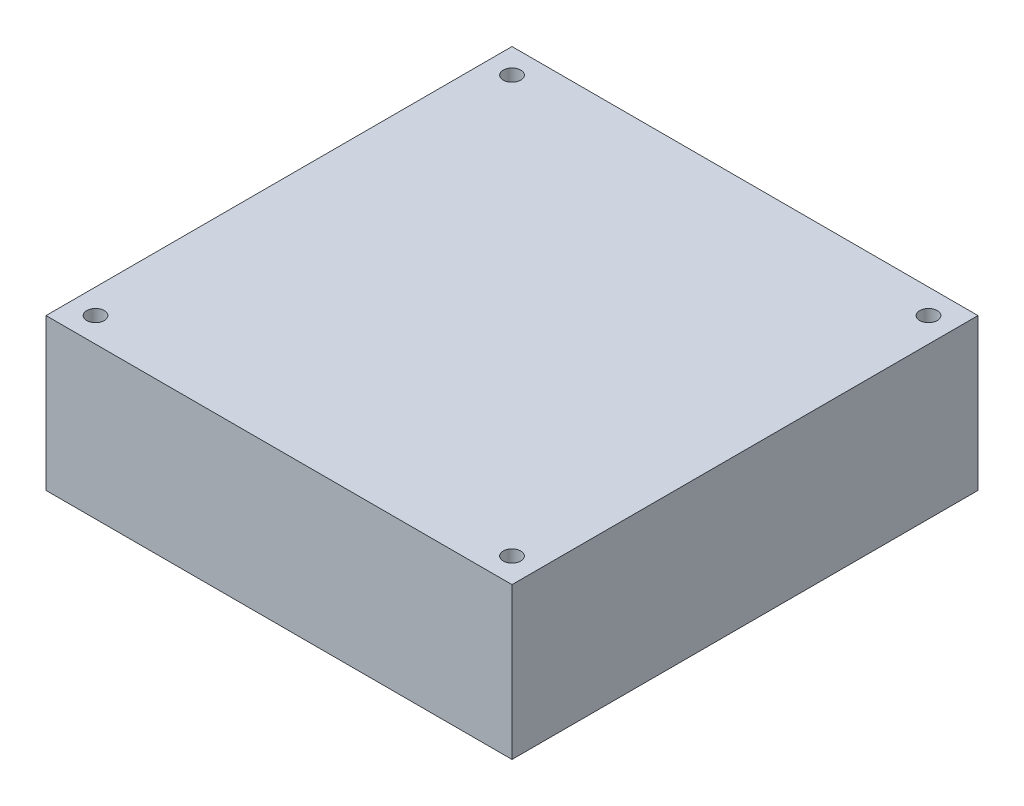
SolidWorks part; units mm, degrees
ref_plane "Front Plane" through (0, 0, 0) normal (0, 0, 1) x (1, 0, 0)
ref_plane "Top Plane" through (0, 0, 0) normal (0, 1, 0) x (1, 0, 0)
ref_plane "Right Plane" through (0, 0, 0) normal (1, 0, 0) x (0, 0, -1)
sketch "Sketch1" plane through (0, 0, 0) normal (0, 1, 0) x (1, 0, 0)
  line L1 (-40, -40) -> (40, -40)
  line L2 (-40, -40) -> (-40, 40)
  line L3 (-40, 40) -> (40, 40)
  line L4 (40, -40) -> (40, 40)
  line L5 (-40, -40) -> (40, 40) construction
  line L6 (-40, 40) -> (40, -40) construction
  line L7 (-35.75, -35.75) -> (35.75, -35.75) construction
  line L8 (-35.75, -35.75) -> (-35.75, 35.75) construction
  line L9 (-35.75, 35.75) -> (35.75, 35.75) construction
  line L10 (35.75, -35.75) -> (35.75, 35.75) construction
  line L11 (-35.75, -35.75) -> (35.75, 35.75) construction
  line L12 (-35.75, 35.75) -> (35.75, -35.75) construction
  circle A0 centre (35.75, 35.75) radius 1.5
  circle A1 centre (-35.75, 35.75) radius 1.5
  circle A2 centre (-35.75, -35.75) radius 1.5
  circle A3 centre (35.75, -35.75) radius 1.5
  point P0 (0, 0)
  point P5 (0, 0)
  dimension "D4" = 3
  dimension "D1" = 80
  dimension "D2" = 80
  dimension "D3" = 71.5
extrude "Boss-Extrude1" add sketch "Sketch1" along normal blind 26
